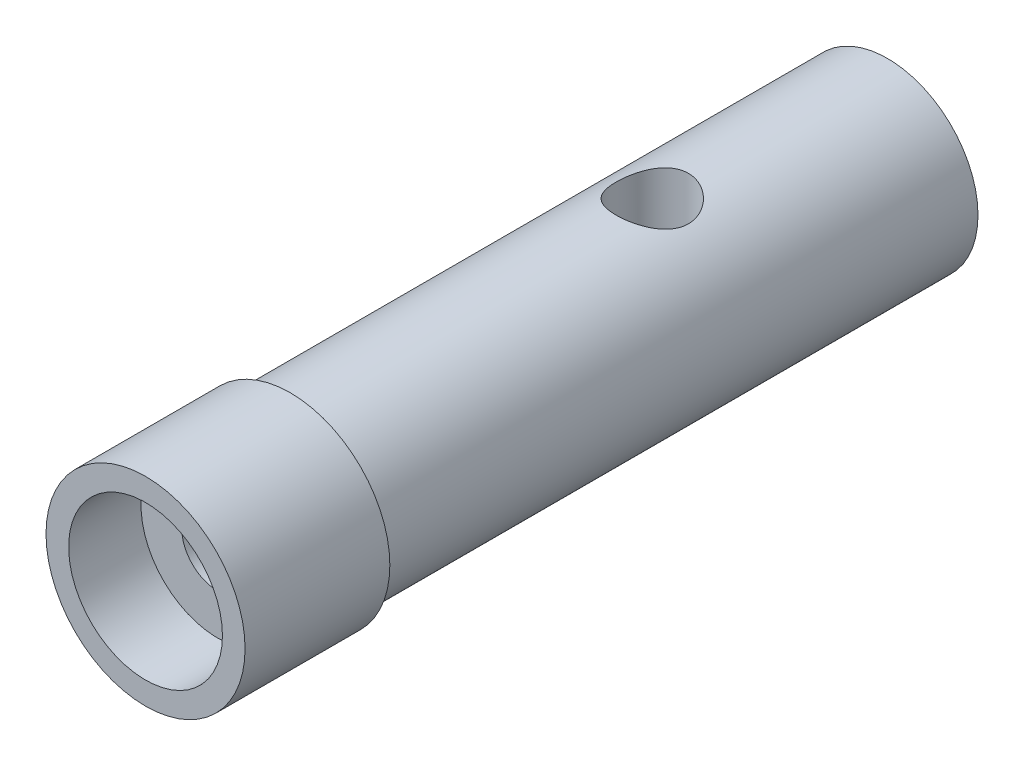
SolidWorks part; units mm, degrees
ref_plane "Front Plane" through (0, 0, 0) normal (0, 0, 1) x (1, 0, 0)
ref_plane "Top Plane" through (0, 0, 0) normal (0, 1, 0) x (1, 0, 0)
ref_plane "Right Plane" through (0, 0, 0) normal (1, 0, 0) x (0, 0, -1)
sketch "Sketch1" plane through (0, 0, 0) normal (0, 1, 0) x (1, 0, 0)
  line L0 (5.5, 0) -> (0, 0)
  line L1 (0, 0) -> (0, -8)
  line L2 (0, -8) -> (5.5, -8)
  line L3 (5.5, -8) -> (5.5, 0)
  line L4 (0, 0) -> (0, -8) construction
revolve "Revolve1" add sketch "Sketch1" angle 360 about L4
sketch "Sketch2" plane through (0, 0, 0) normal (0, 0, -1) x (-1, 0, 0)
  circle A0 centre (0, 0) radius 5
  dimension "D1" = 10
extrude "Boss-Extrude1" add sketch "Sketch2" along normal blind 33
hole_wizard "CBORE for M3.5 Hex Head Machine Screw1" positions "Sketch4" profile "Sketch3" counterbore size "M3.5" standard "ANSI Metric"
sketch "Sketch4" plane through (0, 0, 8) normal (0, 0, 1) x (1, 0, 0)
  point P0 (0, 0)
sketch "Sketch3" plane through (0, 0, 8) normal (1, 0, 0) x (0, -1, 0)
  line L0 (0, 0) -> (0, 14)
  line L1 (0, 14) -> (2, 14)
  line L2 (2, 14) -> (2, 4)
  line L3 (2, 4) -> (4.25, 4)
  line L4 (4.25, 4) -> (4.25, 0)
  line L5 (4.25, 0) -> (0, 0)
  line L10 (0, 14) -> (-2, 14) construction
  line L11 (0, -6.35) -> (0, 107.95) construction
  dimension "Hole Dia." = 4
  dimension "Hole Depth" = 14
  dimension "C'Bore Dia." = 8.5
  dimension "C'Bore Depth" = 4
  dimension "Drill Angle" = 180
hole_wizard "Hole1" positions "3DSketch1" profile "Sketch5" legacy
sketch3d "3DSketch1"
  point P0 (-5.5, 0, 1.5)
sketch "Sketch5" plane through (-5.5, 0, 1.5) normal (0, 1, 0) x (0, 0, 1)
  line L0 (0, 0) -> (0, 3.5)
  line L1 (0, 3.5) -> (1, 3.5)
  line L2 (1, 3.5) -> (1, 0)
  line L3 (1, 0) -> (0, 0)
  line L4 (0, 110) -> (0, -10) construction
  dimension "Diameter" = 2
  dimension "Depth" = 3.5
sketch "Sketch6" plane through (0, 0, -33) normal (0, 0, -1) x (-1, 0, 0)
  circle A0 centre (0, 0) radius 2
  circle A1 centre (0, 0) radius 5
  dimension "D1" = 4
  dimension "D2" = 10
extrude "Cut-Extrude1" cut sketch "Sketch6" against normal blind 10 contours A0
ref_plane "Plane1" through (0, 5, 0) normal (0, 1, 0) x (1, 0, 0)
sketch "Sketch7" plane through (0, 5, 0) normal (0, 1, 0) x (1, 0, 0)
  line L0 (5, 33) -> (-5, 33) construction
  circle A0 centre (0, 20) radius 2
  dimension "D1" = 4
  dimension "D2" = 13
extrude "Cut-Extrude2" cut sketch "Sketch7" against normal blind 5
